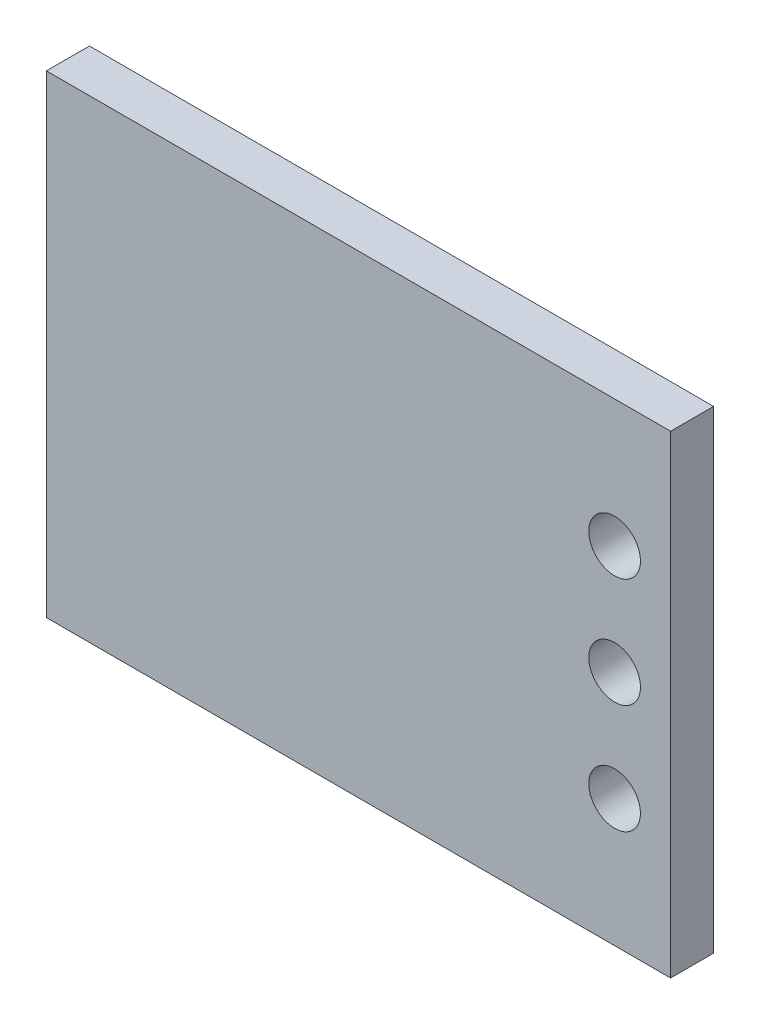
SolidWorks part; units mm, degrees
material "Лист Д16А.Т хх ГОСТ 21631-76"
ref_plane "Front" through (0, 0, 0) normal (0, 0, 1) x (1, 0, 0)
ref_plane "Top" through (0, 0, 0) normal (0, 1, 0) x (1, 0, 0)
ref_plane "Right" through (0, 0, 0) normal (1, 0, 0) x (0, 0, -1)
sketch "Эскиз1" plane through (0, 0, 0) normal (0, 0, 1) x (1, 0, 0)
  line L1 (7.25, -5.5) -> (-7.25, -5.5)
  line L2 (7.25, -5.5) -> (7.25, 5.5)
  line L3 (7.25, 5.5) -> (-7.25, 5.5)
  line L4 (-7.25, -5.5) -> (-7.25, 5.5)
  line L5 (0, 5.5) -> (0, -5.5) construction
  line L6 (7.25, 0) -> (-7.25, 0) construction
  circle A0 centre (5.95, 0) radius 0.6
  circle A1 centre (5.95, 2.54) radius 0.6
  circle A2 centre (5.95, -2.54) radius 0.6
  point P0 (0, 0)
  dimension "D3" = 2.54
  dimension "D4" = 1.2
  dimension "D5" = 1.3
  dimension "D1" = 14.5
  dimension "D2" = 11
extrude "Бобышка-Вытянуть1" add sketch "Эскиз1" along normal blind 1
